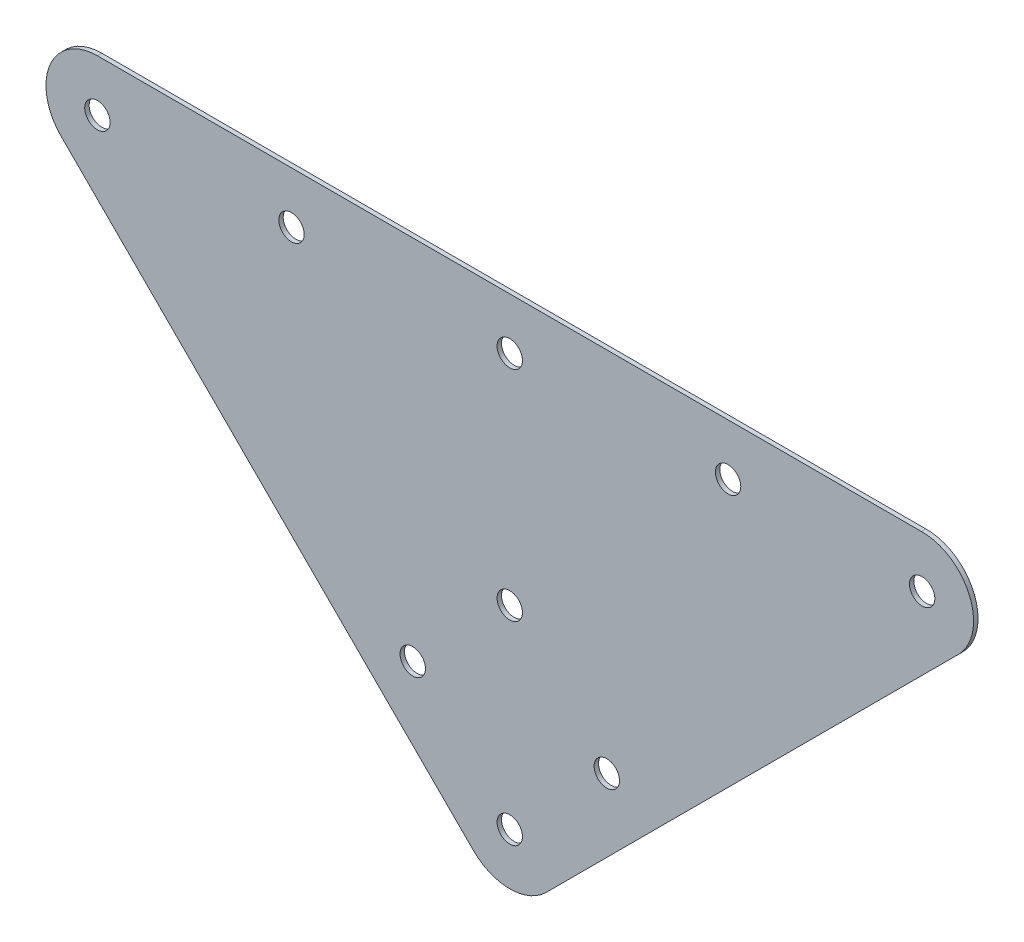
SolidWorks part; units mm, degrees
ref_plane "Front Plane" through (0, 0, 0) normal (0, 0, 1) x (1, 0, 0)
ref_plane "Top Plane" through (0, 0, 0) normal (0, 1, 0) x (1, 0, 0)
ref_plane "Right Plane" through (0, 0, 0) normal (1, 0, 0) x (0, 0, -1)
sketch "Sketch1" plane through (0, 0, 0) normal (0, 0, 1) x (1, 0, 0)
  line L0 (0, 0) -> (-46.2695, 0) construction
  line L1 (-198.6551, -198.6551) -> (-185.1847, -185.1847) construction
  line L2 (-198.6551, 0) -> (-198.6551, -198.6551) construction
  line L3 (-198.6551, -198.6551) -> (-212.1255, -185.1847) construction
  line L4 (-198.6551, -19.05) -> (-279.4774, -19.05) construction
  line L5 (-438.6608, -38.1) -> (83.6453, -38.1) construction
  line L6 (-198.6551, -19.05) -> (-117.8328, -19.05) construction
  line L7 (-279.4774, -19.05) -> (-351.3195, -19.05) construction
  line L8 (-117.8328, -19.05) -> (-45.9908, -19.05) construction
  line L9 (-198.6551, -198.6551) -> (-198.6551, -171.7144) construction
  line L10 (-198.6551, -171.7144) -> (-162.7341, -135.7933) construction
  line L11 (-198.6551, -171.7144) -> (-234.5761, -135.7933) construction
  line L12 (-234.5761, -135.7933) -> (-198.6551, -99.8723) construction
  line L13 (-162.7341, -135.7933) -> (-198.6551, -99.8723) construction
  line L14 (-351.3195, -19.05) -> (-234.5761, -135.7933) construction
  line L15 (-198.6551, -99.8723) -> (-117.8328, -19.05) construction
  line L16 (-162.7341, -135.7933) -> (-45.9908, -19.05) construction
  line L17 (-198.6551, 0) -> (-198.6551, 114.021) construction
  line L18 (-32.7175, -32.7175) -> (0, 0) construction
  line L19 (-46.2695, 0) -> (-351.3195, 0)
  line L20 (-351.3195, 0) -> (-397.3102, 0) construction
  line L21 (-364.7899, -32.5204) -> (-397.3102, 0) construction
  line L22 (-212.1255, -185.1847) -> (-364.7899, -32.5204)
  line L23 (-185.1847, -185.1847) -> (-32.7175, -32.7175)
  circle A0 centre (-198.6551, -19.05) radius 4.699
  circle A1 centre (-279.4774, -19.05) radius 4.699
  circle A2 centre (-117.8328, -19.05) radius 4.699
  circle A3 centre (-351.3195, -19.05) radius 4.699
  circle A4 centre (-45.9908, -19.05) radius 4.699
  circle A5 centre (-351.3195, -19.05) radius 19.05 construction
  circle A6 centre (-45.9908, -19.05) radius 19.05 construction
  circle A7 centre (-198.6551, -171.7144) radius 4.699
  circle A8 centre (-198.6551, -171.7144) radius 19.05 construction
  circle A9 centre (-162.7341, -135.7933) radius 4.699
  circle A10 centre (-162.7341, -135.7933) radius 19.05 construction
  circle A11 centre (-234.5761, -135.7933) radius 4.699
  circle A12 centre (-198.6551, -99.8723) radius 4.699
  arc A13 (-364.7899, -32.5204) -> (-351.3195, 0) centre (-351.3195, -19.05) cw
  arc A14 (-46.2695, 0) -> (-32.7175, -32.7175) centre (-45.9908, -19.05) cw
  arc A15 (-212.1255, -185.1847) -> (-185.1847, -185.1847) centre (-198.6551, -171.7144) ccw
  point P40 (-364.7899, -32.5204)
  dimension "D2" = 9.398
  dimension "D3" = 88.9
  dimension "D4" = 38.1
  dimension "D5" = 165.1
  dimension "D1" = 397.3102
  dimension "D6" = 45
extrude "Boss-Extrude3" add sketch "Sketch1" along normal blind 1.6418 contours A4 | A2 | A0 | A1 | A9 | A7 | A11 | A12 | A3 | L23 A14 L19 A13 L22 A15
